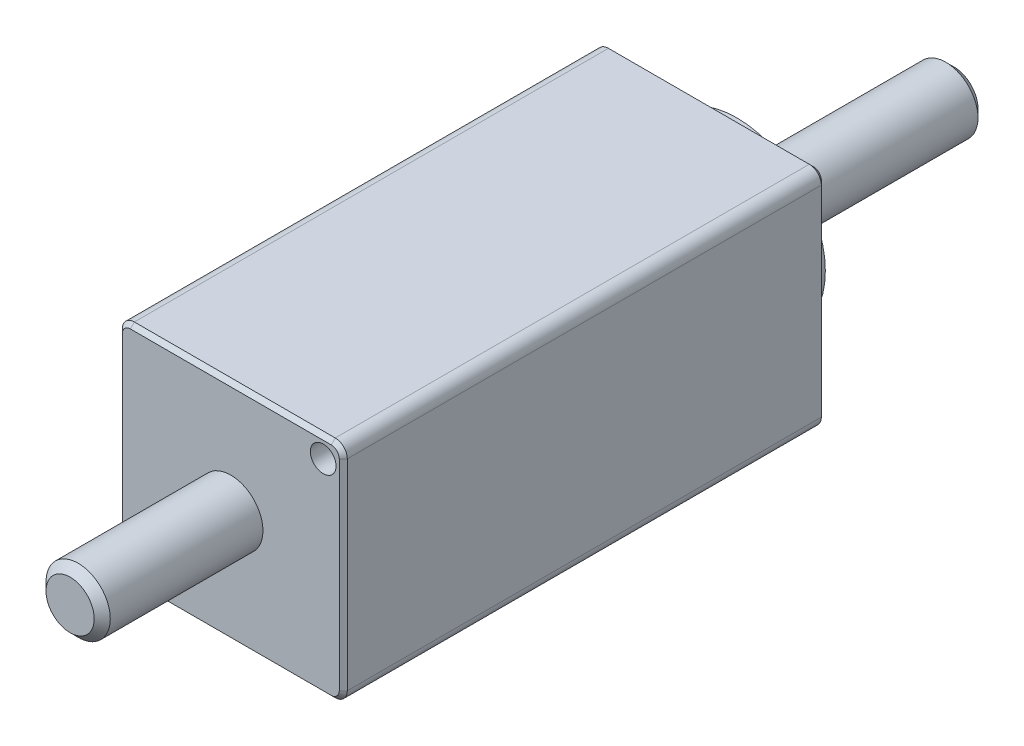
SolidWorks part; units mm, degrees
ref_plane "Front Plane" through (0, 0, 0) normal (0, 0, 1) x (1, 0, 0)
ref_plane "Top Plane" through (0, 0, 0) normal (0, 1, 0) x (1, 0, 0)
ref_plane "Right Plane" through (0, 0, 0) normal (1, 0, 0) x (0, 0, -1)
sketch "Sketch1" plane through (0, 0, 0) normal (0, 0, 1) x (1, 0, 0)
  line L1 (-7, 7) -> (7, 7)
  line L2 (-7, 7) -> (-7, -7)
  line L3 (-7, -7) -> (7, -7)
  line L4 (7, 7) -> (7, -7)
  line L5 (-7, 7) -> (7, -7) construction
  line L6 (-7, -7) -> (7, 7) construction
  point P0 (0, 0)
  dimension "D1" = 14
  dimension "D2" = 14
extrude "Boss-Extrude1" add sketch "Sketch1" along normal blind 30
sketch "Sketch2" plane through (0, 0, 0) normal (0, 0, -1) x (-1, 0, 0)
  circle A0 centre (0, 0) radius 5.5
  dimension "D1" = 11
extrude "Boss-Extrude2" add sketch "Sketch2" along normal blind 1.5
sketch "Sketch3" plane through (0, 0, -1.5) normal (0, 0, -1) x (-1, 0, 0)
  circle A0 centre (0, 0) radius 2
  dimension "D1" = 4
extrude "Boss-Extrude4" add sketch "Sketch3" along normal offset from surface (13.5 mm away) 15 up to face at (5.5, 0, 0) offset beyond the face yes
sketch "Sketch4" plane through (0, 0, 30) normal (0, 0, 1) x (1, 0, 0)
  circle A0 centre (0, 0) radius 2
  dimension "D1" = 4
extrude "Boss-Extrude5" [suppressed] add sketch "Sketch4" along normal blind 10
sketch "Sketch7" plane through (0, 0, 30) normal (0, 0, 1) x (1, 0, 0)
  circle A0 centre (0, 0) radius 2
  dimension "D1" = 4
extrude "Boss-Extrude6" add sketch "Sketch7" along normal blind 10
chamfer "Chamfer1" distance 0.5 angle 45 2 edges at (2, 0, -15) (2, 0, 40)
hole_wizard "M2x0.4 Tapped Hole1" positions "Sketch5" profile "Sketch6" tap size "M2x0.4" standard "ANSI Metric"
sketch "Sketch5" plane through (0, 0, 0) normal (0, 0, -1) x (-1, 0, 0)
  line L0 (-5.75, 5.75) -> (5.75, -5.75)
  line L3 (5.75, 5.75) -> (-5.75, -5.75)
  point P0 (5.75, 5.75)
  point P2 (-5.75, 5.75)
  point P4 (-5.75, -5.75)
  point P6 (5.75, -5.75)
  dimension "D1" = 11.5
  dimension "D2" = 11.5
sketch "Sketch6" plane through (-5.75, 5.75, 0) normal (1, 0, 0) x (0, 1, 0)
  line L0 (0, 0) -> (0, 4.8807)
  line L1 (0, 4.8807) -> (0.8, 4.4)
  line L2 (0.8, 4.4) -> (0.8, 0)
  line L5 (0.8, 0) -> (0, 0)
  line L10 (0, 4.8807) -> (-0.8, 4.4) construction
  line L11 (0, -6.35) -> (0, 107.95) construction
  dimension "Tap Drill Dia." = 1.6
  dimension "Tap Drill Depth" = 4.4
  dimension "Drill Angle" = 118
cosmetic thread "Hole Thread1" parameters "D1"=3.2, "D2"=2
cosmetic thread "Hole Thread2" parameters "D1"=3.2, "D2"=2
cosmetic thread "Hole Thread3" parameters "D1"=3.2, "D2"=2
cosmetic thread "Hole Thread4" parameters "D1"=3.2, "D2"=2
fillet "Fillet1" radius 0.75 4 edges at (7, 7, 15) (7, -7, 15) (-7, -7, 15) (-7, 7, 15)
chamfer "Chamfer2" distance 0.25 angle 45 8 edges at (7, 0, 30) (6.7803, 6.7803, 30) (6.7803, -6.7803, 30) (0, 7, 30) (0, -7, 30) (-6.7803, 6.7803, 30) (-6.7803, -6.7803, 30) (-7, 0, 30)
hole_wizard "M2x0.4 Tapped Hole2" positions "Sketch8" profile "Sketch9" tap size "M2x0.4" standard "ANSI Metric"
sketch "Sketch8" plane through (0, 0, 30) normal (0, 0, 1) x (1, 0, 0)
  circle A0 centre (5.75, 5.75) radius 0.8 construction
  circle A1 centre (-5.75, -5.75) radius 0.8 construction
  point P0 (5.75, 5.75)
  point P2 (-5.75, -5.75)
  point P4 (0, 0)
  point P7 (0, 0)
sketch "Sketch9" plane through (5.75, 5.75, 30) normal (1, 0, 0) x (0, -1, 0)
  line L0 (0, 0) -> (0, 4.8807)
  line L1 (0, 4.8807) -> (0.8, 4.4)
  line L2 (0.8, 4.4) -> (0.8, 0)
  line L5 (0.8, 0) -> (0, 0)
  line L10 (0, 4.8807) -> (-0.8, 4.4) construction
  line L11 (0, -6.35) -> (0, 107.95) construction
  dimension "Tap Drill Dia." = 1.6
  dimension "Tap Drill Depth" = 4.4
  dimension "Drill Angle" = 118
cosmetic thread "Hole Thread5" parameters "D1"=3.2, "D2"=2
cosmetic thread "Hole Thread6" parameters "D1"=3.2, "D2"=2
